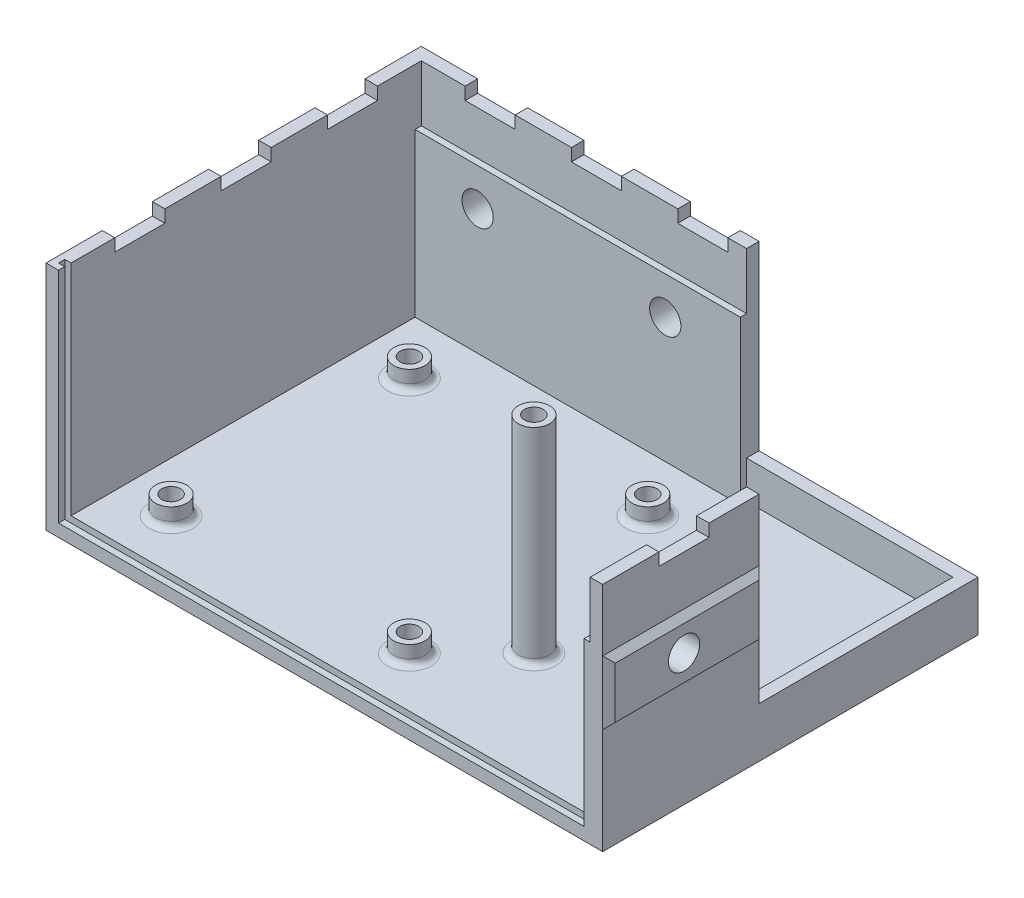
SolidWorks part; units mm, degrees
ref_plane "前视基准面" through (0, 0, 0) normal (0, 0, 1) x (1, 0, 0)
ref_plane "上视基准面" through (0, 0, 0) normal (0, 1, 0) x (1, 0, 0)
ref_plane "右视基准面" through (0, 0, 0) normal (1, 0, 0) x (0, 0, -1)
sketch "底座图" plane through (0, 0, 0) normal (0, 1, 0) x (1, 0, 0)
  line L1 (0, 60) -> (89, 60)
  line L2 (0, 60) -> (0, 0)
  line L3 (0, 0) -> (89, 0)
  line L4 (89, 60) -> (89, 0)
  dimension "D1" = 60
  dimension "D2" = 89
extrude "底座" add sketch "底座图" along normal blind 2
sketch "螺丝柱图" plane through (0, 2, 0) normal (0, 1, 0) x (1, 0, 0)
  line L1 (0, 0) -> (89, 0) construction
  line L3 (0, 60) -> (0, 0) construction
  circle A0 centre (10, 10) radius 2.5
  circle A1 centre (48.1, 10) radius 2.5
  circle A2 centre (48.1, 48.1) radius 2.5
  circle A3 centre (10, 48.1) radius 2.5
  dimension "D5" = 38.1
  dimension "D7" = 5
  dimension "D1" = 10
  dimension "D2" = 10
  dimension "D4" = 2
  dimension "D6" = 38.1
  dimension "D3" = 2
extrude "螺丝柱" add sketch "螺丝柱图" along normal blind 3
sketch "螺丝柱孔图" plane through (0, 5, 0) normal (0, 1, 0) x (1, 0, 0)
  circle A1 centre (48.1, 10) radius 1.5
  circle A2 centre (10, 10) radius 1.5
  circle A3 centre (10, 10) radius 1.5
  circle A4 centre (10, 48.1) radius 1.5
  circle A5 centre (48.1, 48.1) radius 1.5
  dimension "D1" = 1
  dimension "D2" = 2
  dimension "D3" = 2
extrude "螺丝柱孔" cut sketch "螺丝柱孔图" against normal through all
sketch "顶盖螺丝柱图" plane through (0, 2, 0) normal (0, 1, 0) x (1, 0, 0)
  line L1 (0, 0) -> (89, 0) construction
  circle A0 centre (58, 20) radius 2.5
  circle A1 centre (10, 10) radius 2.5 construction
  dimension "D1" = 5
  dimension "D2" = 48
  dimension "D3" = 20
extrude "顶盖螺丝柱" add sketch "顶盖螺丝柱图" along normal blind 33
sketch "顶盖螺丝孔图" plane through (0, 35, 0) normal (0, 1, 0) x (1, 0, 0)
  circle A0 centre (58, 20) radius 1.5
  dimension "D1" = 3
extrude "顶盖螺丝孔" cut sketch "顶盖螺丝孔图" against normal blind 15
fillet "圆角1" radius 1 5 edges at (10, 2, -7.5) (48.1, 2, -7.5) (48.1, 2, -45.6) (58, 2, -17.5) (10, 2, -45.6)
sketch "侧壁图" plane through (0, 2, 0) normal (0, 1, 0) x (1, 0, 0)
  line L8 (2, 58) -> (2, 2)
  line L9 (2, 2) -> (87, 2)
  line L10 (87, 2) -> (87, 58)
  line L11 (87, 58) -> (2, 58)
  line L12 (2, 58) -> (2, 0)
  line L14 (87, 0) -> (87, 58)
  line L15 (87, 58) -> (2, 58)
  dimension "D1" = 2
extrude "侧壁" add sketch "侧壁图" along normal blind 35 thin
sketch "连接件缺口图" plane through (0, 37, 0) normal (0, 1, 0) x (1, 0, 0)
  line L1 (89, 60) -> (54, 60)
  line L2 (89, 60) -> (89, 25)
  line L3 (89, 25) -> (54, 25)
  line L4 (54, 60) -> (54, 25)
  dimension "D1" = 35
  dimension "D2" = 35
extrude "连接件缺口处" cut sketch "连接件缺口图" against normal blind 29
sketch "草图8" plane through (87, 0, 0) normal (-1, 0, 0) x (0, 0, 1)
  line L0 (-25, 8) -> (-25, 37) construction
  line L1 (-25, 28) -> (0, 28)
  line L2 (-25, 28) -> (-25, 2)
  line L3 (-25, 2) -> (0, 2)
  line L4 (0, 28) -> (0, 2)
  line L6 (0, 37) -> (-25, 37) construction
  line L7 (0, 2) -> (-58, 2) construction
  dimension "D1" = 9
  dimension "D2" = 0
extrude "内凸层（侧）" add sketch "草图8" along normal blind 1
sketch "安装纹路图（侧）" plane through (89, 0, 0) normal (1, 0, 0) x (0, 0, -1)
  line L0 (0, 37) -> (0, 0) construction
  line L1 (0, 27.1) -> (25, 27.1)
  line L2 (0, 27.1) -> (0, 16.9)
  line L3 (0, 16.9) -> (25, 16.9)
  line L4 (25, 27.1) -> (25, 16.9)
  line L5 (25, 8) -> (25, 37) construction
  line L6 (0, 37) -> (25, 37) construction
  dimension "D1" = 9.9
  dimension "D2" = 10.2
extrude "安装纹路（侧）" add sketch "安装纹路图（侧）" along normal blind 1 draft 45
sketch "草图10" plane through (86, 0, 0) normal (-1, 0, 0) x (0, 0, 1)
  line L0 (0, 37) -> (-25, 37) construction
  line L4 (0, 2) -> (0, 28) construction
  circle A0 centre (-12, 22) radius 2.5
  dimension "D1" = 5
  dimension "D2" = 15
  dimension "D3" = 12
extrude "安装孔（侧）" cut sketch "草图10" against normal through all
sketch "草图7" plane through (0, 0, -58) normal (0, 0, 1) x (1, 0, 0)
  line L0 (54, 37) -> (54, 8) construction
  line L1 (54, 28) -> (2, 28)
  line L2 (54, 28) -> (54, 1.925)
  line L3 (54, 1.925) -> (2, 1.925)
  line L4 (2, 28) -> (2, 1.925)
  line L5 (2, 37) -> (2, 2) construction
  line L7 (54, 37) -> (2, 37) construction
  dimension "D1" = 9
extrude "内凸层（后）" add sketch "草图7" along normal blind 1
sketch "安装纹路图（后）" plane through (0, 0, -60) normal (0, 0, -1) x (-1, 0, 0)
  line L0 (-54, 8) -> (-54, 37) construction
  line L1 (-54, 27.1) -> (0, 27.1)
  line L2 (-54, 27.1) -> (-54, 16.9)
  line L3 (-54, 16.9) -> (0, 16.9)
  line L4 (0, 27.1) -> (0, 16.9)
  line L5 (0, 37) -> (0, 0) construction
  line L6 (-54, 37) -> (0, 37) construction
  dimension "D1" = 9.9
  dimension "D2" = 10.2
extrude "安装纹路（后）" add sketch "安装纹路图（后）" along normal blind 1 draft 45
sketch "安装孔图（后）" plane through (0, 0, -57) normal (0, 0, 1) x (1, 0, 0)
  line L0 (2, 28) -> (2, 2) construction
  line L2 (54, 37) -> (2, 37) construction
  circle A0 centre (12, 22) radius 2.5
  circle A1 centre (42, 22) radius 2.5
  dimension "D1" = 10
  dimension "D2" = 5
  dimension "D5" = 30
  dimension "D3" = 15
  dimension "D4" = 2
extrude "安装孔（后）" cut sketch "安装孔图（后）" against normal through all
sketch "前盖卡槽图（下）" plane through (0, 2, 0) normal (0, 1, 0) x (1, 0, 0)
  line L0 (2, 58) -> (2, 0) construction
  line L1 (2, 2) -> (86, 2)
  line L2 (2, 2) -> (2, 1)
  line L3 (2, 1) -> (86, 1)
  line L4 (86, 2) -> (86, 1)
  line L5 (86, 25) -> (86, 0) construction
  line L6 (2, 0) -> (86, 0) construction
  dimension "D1" = 1
  dimension "D2" = 1
extrude "前盖卡槽（下）" cut sketch "前盖卡槽图（下）" against normal blind 1
sketch "前盖卡槽图（外）" plane through (2, 0, 0) normal (1, 0, 0) x (0, 0, -1)
  line L0 (58, 37) -> (0, 37) construction
  line L1 (2, 37) -> (1, 37)
  line L2 (2, 37) -> (2, 1)
  line L3 (2, 1) -> (1, 1)
  line L4 (1, 37) -> (1, 1)
  line L5 (0, 37) -> (0, 2) construction
  line L6 (2, 1) -> (1, 1) construction
  point P8 (1.5, 1)
  dimension "D1" = 1
  dimension "D2" = 1
  dimension "D3" = 0
extrude "前盖卡槽（外）" cut sketch "前盖卡槽图（外）" against normal blind 1
sketch "前盖卡槽图（侧）" plane through (86, 0, 0) normal (-1, 0, 0) x (0, 0, 1)
  line L0 (0, 28) -> (-25, 28) construction
  line L1 (-2, 28) -> (-1, 28)
  line L2 (-2, 28) -> (-2, 1)
  line L3 (-2, 1) -> (-1, 1)
  line L4 (-1, 28) -> (-1, 1)
  line L5 (0, 2) -> (0, 28) construction
  line L6 (-1, 1) -> (-2, 1) construction
  dimension "D1" = 1
  dimension "D2" = 1
  dimension "D3" = 0
extrude "前盖卡槽（侧）" cut sketch "前盖卡槽图（侧）" against normal blind 1
sketch "草图26" plane through (0, 37, 0) normal (0, 1, 0) x (1, 0, 0)
  line L0 (87, 0) -> (87, 25) construction
  line L1 (87, 9) -> (89, 9)
  line L2 (87, 9) -> (87, 17)
  line L3 (87, 17) -> (89, 17)
  line L4 (89, 9) -> (89, 17)
  line L5 (89, 0) -> (89, 25) construction
  line L6 (89, 0) -> (87, 0) construction
  dimension "D1" = 9
  dimension "D2" = 8
extrude "顶盖卡槽（侧）" cut sketch "草图26" against normal blind 2
sketch "顶盖卡槽图（外）" plane through (0, 37, 0) normal (0, 1, 0) x (1, 0, 0)
  line L0 (0, 60) -> (0, 0) construction
  line L1 (0, 9) -> (2, 9)
  line L2 (0, 9) -> (0, 17)
  line L3 (0, 17) -> (2, 17)
  line L4 (2, 9) -> (2, 17)
  line L5 (2, 57) -> (2, 2) construction
  line L6 (2, 0) -> (0, 0) construction
  line L7 (2, 26) -> (2, 34)
  line L8 (0, 34) -> (2, 34)
  line L9 (0, 26) -> (0, 34)
  line L10 (0, 26) -> (2, 26)
  line L11 (2, 43) -> (2, 51)
  line L12 (0, 51) -> (2, 51)
  line L13 (0, 43) -> (0, 51)
  line L14 (0, 43) -> (2, 43)
  line L15 (54, 60) -> (0, 60) construction
  line L16 (9, 60) -> (17, 60)
  line L17 (9, 60) -> (9, 58)
  line L18 (9, 58) -> (17, 58)
  line L19 (17, 60) -> (17, 58)
  line L20 (54, 58) -> (2, 58) construction
  line L21 (26, 60) -> (34, 60)
  line L22 (26, 60) -> (26, 58)
  line L23 (26, 58) -> (34, 58)
  line L24 (34, 60) -> (34, 58)
  line L25 (43, 60) -> (51, 60)
  line L26 (43, 60) -> (43, 58)
  line L27 (43, 58) -> (51, 58)
  line L28 (51, 60) -> (51, 58)
  dimension "D1" = 9
  dimension "D2" = 8
  dimension "D4" = 9
  dimension "D5" = 8
  dimension "D3" = 3
  dimension "D6" = 3
extrude "顶盖卡槽（外）" cut sketch "顶盖卡槽图（外）" against normal blind 2
